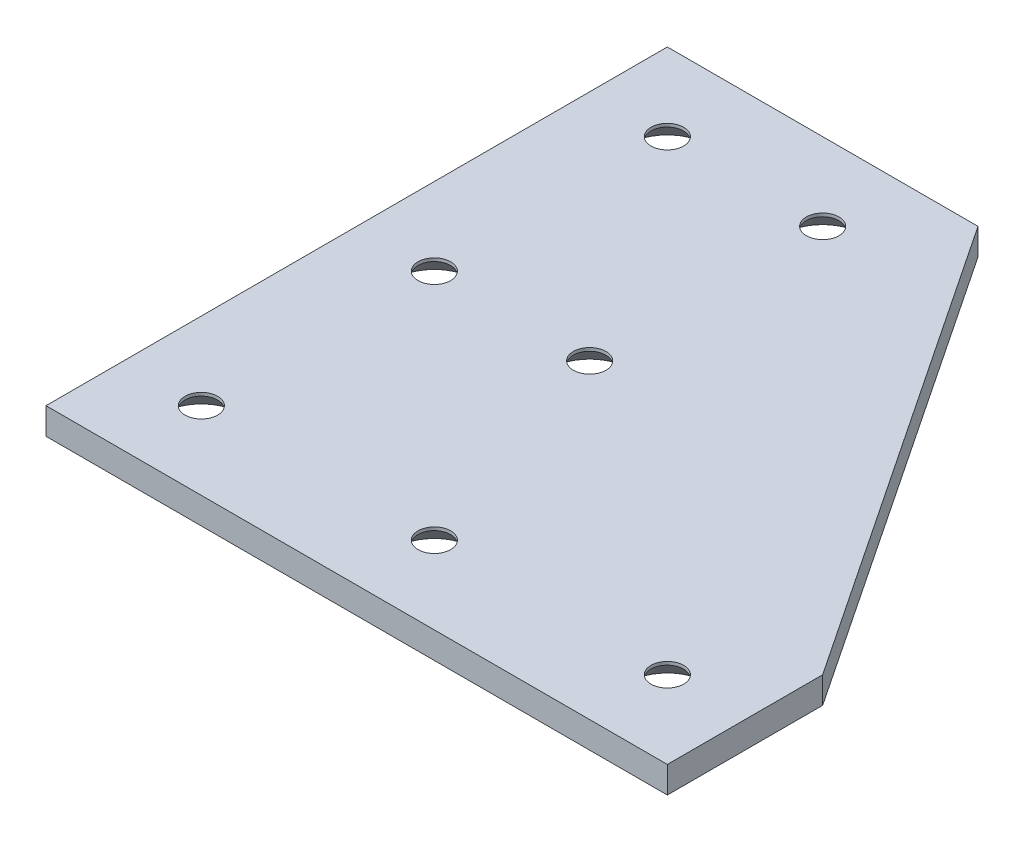
SolidWorks part; units mm, degrees
material "AISI 1010 Steel, hot rolled bar"
ref_plane "Front Plane" through (0, 0, 0) normal (0, 0, 1) x (1, 0, 0)
ref_plane "Top Plane" through (0, 0, 0) normal (0, 1, 0) x (1, 0, 0)
ref_plane "Right Plane" through (0, 0, 0) normal (1, 0, 0) x (0, 0, -1)
sketch "Sketch1" plane through (0, 0, 0) normal (0, 1, 0) x (1, 0, 0)
  line L0 (0, 0) -> (80, 0)
  line L1 (80, 0) -> (80, 20)
  line L2 (80, 20) -> (40, 80)
  line L3 (40, 80) -> (0, 80)
  line L4 (0, 80) -> (0, 0)
  point P8 (0, 80)
  point P11 (40, 80)
  point P14 (80, 20)
  point P17 (80, 0)
  point P20 (0, 0)
  dimension "D1" = 80
  dimension "D2" = 80
  dimension "D3" = 20
  dimension "D4" = 40
extrude "Boss-Extrude1" add sketch "Sketch1" along normal blind 3.416
sketch "Sketch2" plane through (0, 3.416, 0) normal (0, 1, 0) x (1, 0, 0)
  line L0 (0, 0) -> (80, 0) construction
  line L1 (0, 80) -> (0, 0) construction
  line L2 (80, 0) -> (80, 20) construction
  line L3 (40, 80) -> (0, 80) construction
  circle A0 centre (10, 10) radius 2.1
  circle A1 centre (40, 10) radius 2.1
  circle A2 centre (70, 10) radius 2.1
  circle A4 centre (30, 40) radius 2.1
  circle A5 centre (30, 70) radius 2.1
  circle A6 centre (10, 40) radius 2.1
  circle A7 centre (10, 70) radius 2.1
  circle A8 centre (30, 10) radius 2.1 [skipped]
  dimension "D1" = 4.2
  dimension "D3" = 3
  dimension "D2" = 10
  dimension "10" = 10
  dimension "D4" = 10
  dimension "D7" = 10
  dimension "D8" = 10
  dimension "D9" = 20
  dimension "D5" = 2
  dimension "D6" = 3
extrude "Cut-Extrude1" cut sketch "Sketch2" against normal blind 4
chamfer "Chamfer1" distance 3 angle 45 7 edges at (10, 0, -67.9) (30, 0, -67.9) (30, 0, -37.9) (10, 0, -37.9) (10, 0, -7.9) (40, 0, -7.9) (70, 0, -7.9)
fillet "Fillet1" [suppressed] radius 1
